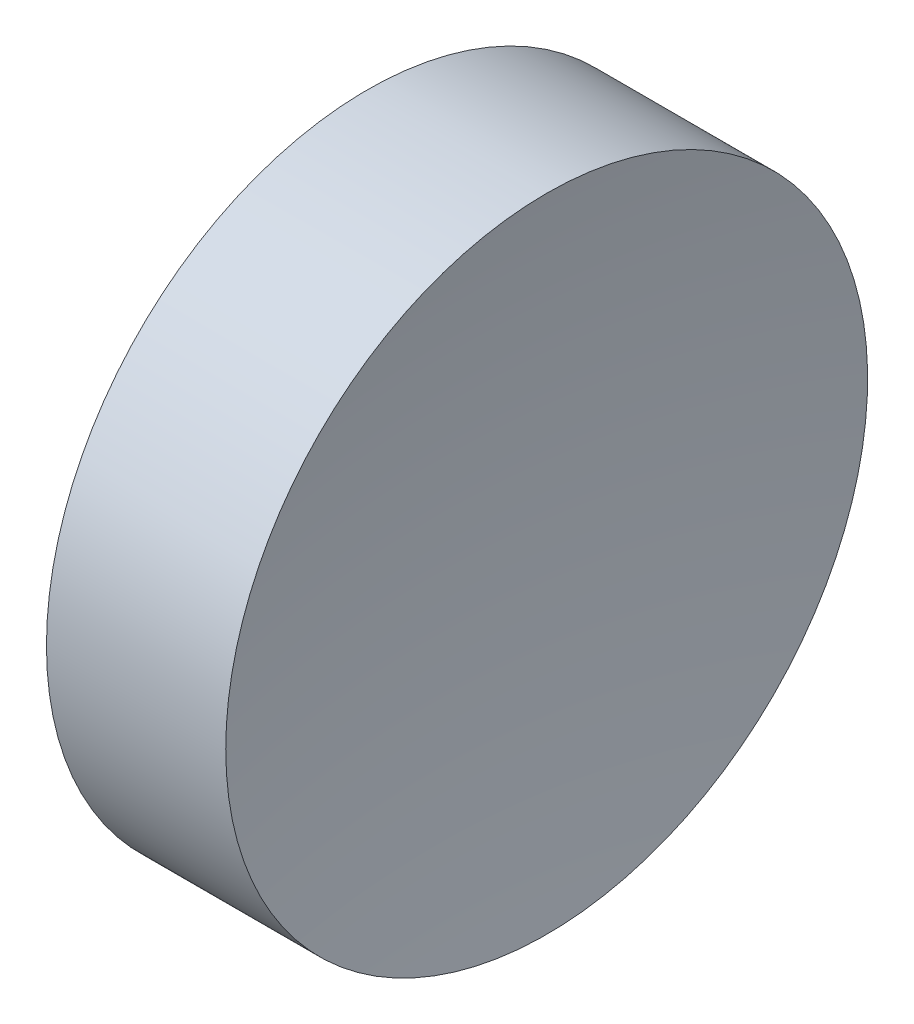
SolidWorks part; units mm, degrees
ref_plane "前视基准面" through (0, 0, 0) normal (0, 0, 1) x (1, 0, 0)
ref_plane "上视基准面" through (0, 0, 0) normal (0, 1, 0) x (1, 0, 0)
ref_plane "右视基准面" through (0, 0, 0) normal (1, 0, 0) x (0, 0, -1)
sketch "草图1" plane through (0, 0, 0) normal (0, 0, 1) x (1, 0, 0)
  line L0 (54.4926, 34.689) -> (66.3882, 34.689) construction
  line L1 (57.5463, 34.689) -> (57.5463, 40.939)
  line L2 (57.5463, 40.939) -> (61.0376, 40.939)
  line L3 (60.5463, 34.689) -> (57.5463, 34.689)
  arc A0 (61.0376, 40.939) -> (60.5463, 34.689) centre (100.5463, 34.689) ccw
  dimension "D1" = 3.4913
revolve "旋转1" add sketch "草图1" angle 360 about L0
